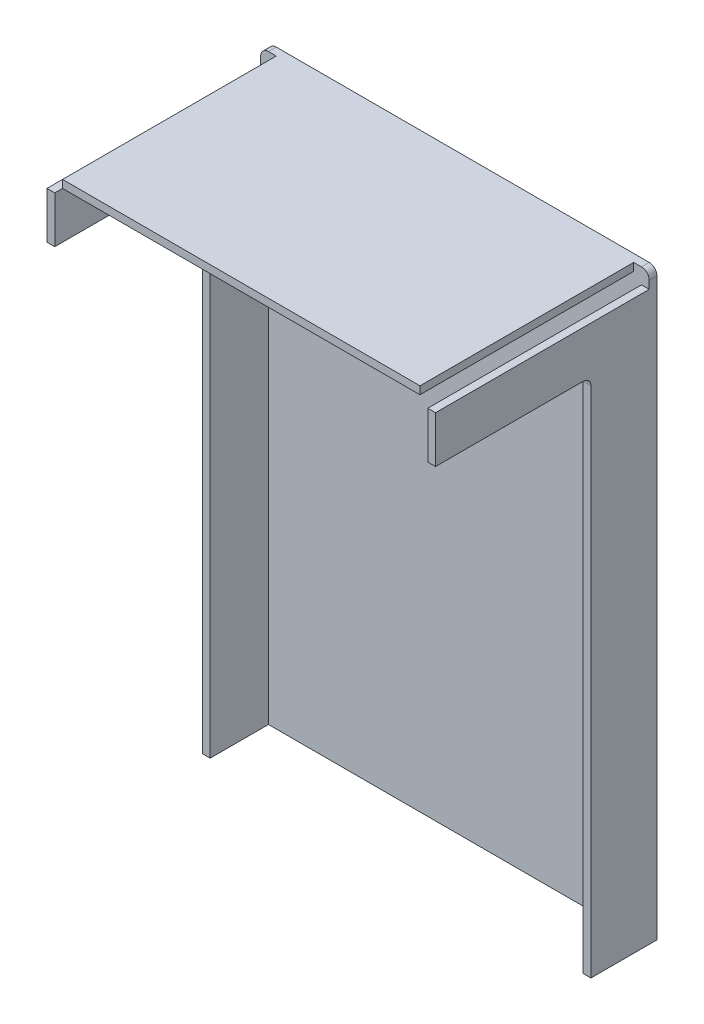
SolidWorks part; units mm, degrees
material "Acrylic (Medium-high impact)"
ref_plane "Front Plane" through (0, 0, 0) normal (0, 0, 1) x (1, 0, 0)
ref_plane "Top Plane" through (0, 0, 0) normal (0, 1, 0) x (1, 0, 0)
ref_plane "Right Plane" through (0, 0, 0) normal (1, 0, 0) x (0, 0, -1)
sketch "Sketch1" plane through (0, 0, 0) normal (0, 0, 1) x (1, 0, 0)
  line L0 (0, 0) -> (127, 0)
  line L1 (127, 0) -> (127, 190.5)
  line L2 (127, 190.5) -> (0, 190.5)
  line L3 (0, 190.5) -> (0, 0)
  dimension "D1" = 127
  dimension "D2" = 190.5
extrude "Boss-Extrude1" add sketch "Sketch1" along normal blind 2.54
sketch "Sketch3" plane through (0, 0, 2.54) normal (0, 0, 1) x (1, 0, 0)
  line L0 (0, 190.5) -> (0, 0)
  line L1 (0, 190.5) -> (0, 0) construction
  line L2 (0, 0) -> (2.54, 0)
  line L3 (2.54, 0) -> (2.54, 187.96)
  line L4 (2.54, 187.96) -> (124.46, 187.96)
  line L5 (124.46, 187.96) -> (124.46, 0)
  line L6 (124.46, 0) -> (127, 0)
  line L7 (127, 0) -> (127, 190.5) construction
  line L8 (127, 0) -> (127, 190.5)
  line L9 (127, 190.5) -> (0, 190.5)
  line L10 (79.5585, 187.96) -> (79.5585, 190.5) construction
  line L11 (124.46, 185.42) -> (127, 185.42)
  line L12 (121.92, 187.96) -> (121.92, 190.5)
  line L13 (5.08, 187.96) -> (5.08, 190.5)
  line L14 (2.54, 185.42) -> (0, 185.42)
  point P24 (121.92, 189.23)
  line M15 (127, 0) -> (127, 190.5)
  line M16 (127, 190.5) -> (0, 190.5)
  dimension "D1" = 2.54
  dimension "D2" = 190.5
  dimension "D3" = 5.08
  dimension "D4" = 5.08
  dimension "D5" = 5.08
  dimension "D6" = 5.08
extrude "Boss-Extrude2" add sketch "Sketch3" along normal blind 19.05 contours L4 L10 L13 M16 | L10 L4 L12 L9 | L11 L5 L6 M15 | L3 L14 L0 L2
sketch "Sketch4" plane through (0, 0, 21.59) normal (0, 0, 1) x (1, 0, 0)
  line L0 (2.54, 0) -> (2.54, 185.42) construction
  line L1 (0, 185.42) -> (2.54, 185.42)
  line L2 (0, 185.42) -> (0, 170.18)
  line L3 (0, 170.18) -> (2.54, 170.18)
  line L4 (2.54, 185.42) -> (2.54, 170.18)
  line L5 (127, 0) -> (127, 185.42) construction
  line L6 (5.08, 190.5) -> (121.92, 190.5)
  line L7 (5.08, 190.5) -> (5.08, 187.96)
  line L8 (5.08, 187.96) -> (121.92, 187.96)
  line L9 (121.92, 190.5) -> (121.92, 187.96)
  line L10 (124.46, 185.42) -> (127, 185.42)
  line L11 (124.46, 185.42) -> (124.46, 170.18)
  line L12 (124.46, 170.18) -> (127, 170.18)
  line L13 (127, 185.42) -> (127, 170.18)
  dimension "D1" = 15.24
extrude "Boss-Extrude3" add sketch "Sketch4" along normal blind 50.8
fillet "Fillet2" radius 2.54 4 edges at (0, 190.5, 1.27) (127, 190.5, 1.27) (1.27, 170.18, 21.59) (125.73, 170.18, 21.59)
